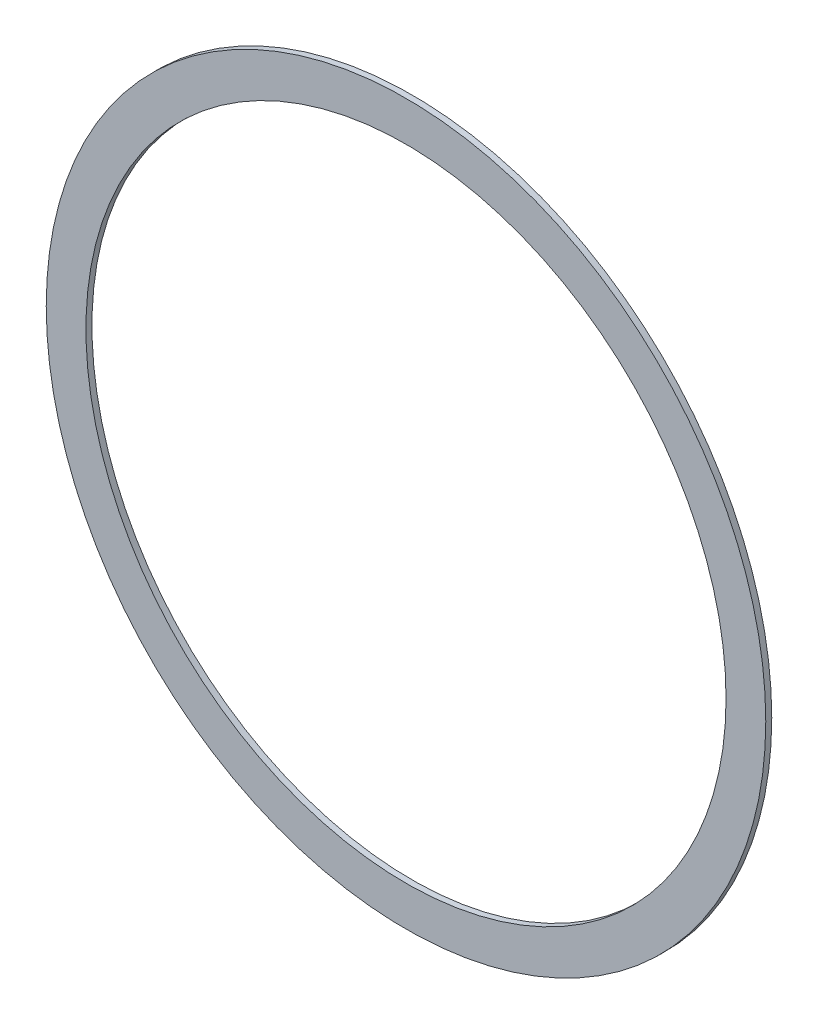
SolidWorks part; units mm, degrees
material "Maple"
ref_plane "Wasteboard" through (0, 0, 0) normal (0, 0, 1) x (1, 0, 0)
ref_plane "Left-Right" through (0, 0, 0) normal (0, 1, 0) x (1, 0, 0)
ref_plane "Front-Back" through (0, 0, 0) normal (1, 0, 0) x (0, 0, -1)
sketch "Sketch2" plane through (0, 0, 0) normal (0, 0, 1) x (1, 0, 0)
  line L0 (0, 0) -> (0, 50000) construction
  circle A0 centre (0, 0) radius 192.8812 construction
  circle A1 centre (0, 0) radius 209.55 construction
  circle A2 centre (0, 0) radius 172.72 construction
  circle A3 centre (0, 0) radius 252.73 construction
  circle A4 centre (0, 0) radius 184.785 construction
  circle A5 centre (0, 0) radius 190.5
  circle A6 centre (0, 0) radius 169.4688
  circle A7 centre (0, 0) radius 194.31 construction
  circle A8 centre (0, 184.785) radius 9.525 construction
  point P14 (0, 172.72)
  point P15 (0, 169.4688)
  point P16 (0, 175.26)
  dimension "D1" = 385.7625
  dimension "D2" = 419.1
  dimension "D3" = 2.54
  dimension "D4" = 505.46
  dimension "D5" = 369.57
  dimension "D6" = 381
  dimension "D7" = 3.2512
  dimension "D8" = 388.62
  dimension "D9" = 19.05
extrude "Boss-Extrude2" add sketch "Sketch2" along normal blind 3.175
